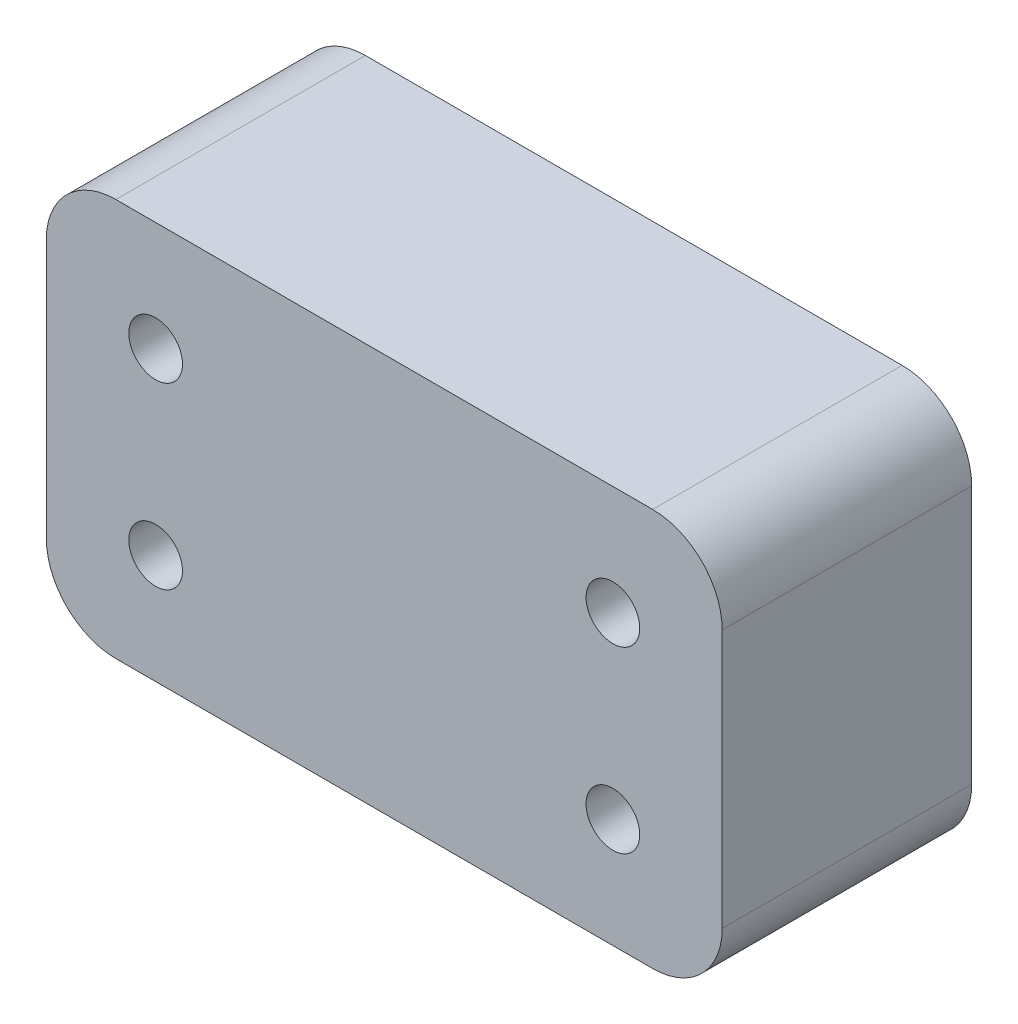
SolidWorks part; units mm, degrees
ref_plane "Front Plane" through (0, 0, 0) normal (0, 0, 1) x (1, 0, 0)
ref_plane "Top Plane" through (0, 0, 0) normal (0, 1, 0) x (1, 0, 0)
ref_plane "Right Plane" through (0, 0, 0) normal (1, 0, 0) x (0, 0, -1)
sketch "Sketch1" plane through (0, 0, 0) normal (0, 0, 1) x (1, 0, 0)
  line L0 (38.9055, 79) -> (-21.0984, 79)
  line L1 (38.9055, 79) -> (38.9055, 47)
  line L4 (-21.0945, 79) -> (-21.0945, 47)
  line L6 (38.9055, 47) -> (-21.0945, 47)
  circle A4 centre (31.9055, 72) radius 2.75 construction
  dimension "D1" = 7
  dimension "D2" = 7
extrude "Boss-Extrude1" add sketch "Sketch1" along normal blind 25.1 contours L6 L1 L0 L4
hole_wizard "M5 Clearance Hole1" positions "Sketch2" profile "Sketch3" hole size "M5" standard "ISO" end condition through all
sketch "Sketch2" plane through (0, 0, 25.1) normal (0, 0, -1) x (-1, 0, 0)
  line L0 (-38.9055, 79) -> (-38.9055, 47) construction
  line L1 (-38.9055, 47) -> (21.0945, 47) construction
  point P0 (-31.9055, 72)
  point P2 (-31.9055, 54)
  point P4 (14.0945, 54)
  point P6 (14.0945, 72)
  dimension "D1" = 46
  dimension "D2" = 18
  dimension "D3" = 46
  dimension "D4" = 18
  dimension "D5" = 7
  dimension "D6" = 7
sketch "Sketch3" plane through (31.9055, 72, 25.1) normal (1, 0, 0) x (0, -1, 0)
  line L0 (0, 0) -> (0, 25.1)
  line L1 (0, 25.1) -> (2.7, 25.1)
  line L2 (2.7, 25.1) -> (2.7, 0)
  line L5 (2.7, 0) -> (0, 0)
  line L11 (0, -6.35) -> (0, 107.95) construction
  dimension "Thru Hole Dia." = 5.4
  dimension "Thru Hole Depth" = 25.1
fillet "Fillet1" radius 3 4 edges at (38.9055, 47, 12.55) (-21.0945, 47, 12.55) (38.9055, 79, 12.55) (-21.0945, 79, 12.55)
sketch "Sketch4" plane through (0, 0, 25.1) normal (0, 0, 1) x (1, 0, 0)
  line L8 (42.9055, 50) -> (42.9055, 76)
  line L9 (35.9055, 83) -> (-18.0945, 83)
  line L10 (-25.0945, 76) -> (-25.0945, 50)
  line L11 (-18.0945, 43) -> (35.9055, 43)
  line L12 (42.9055, 50) -> (42.9055, 76)
  line L13 (35.9055, 83) -> (-18.0945, 83)
  line L14 (-25.0945, 76) -> (-25.0945, 50)
  line L15 (-18.0945, 43) -> (35.9055, 43)
  line L17 (35.9055, 79) -> (-18.0945, 79)
  line L18 (38.9055, 50) -> (38.9055, 76)
  line L19 (-18.0945, 47) -> (35.9055, 47)
  line L20 (-21.0945, 76) -> (-21.0945, 50)
  line L21 (35.9055, 79) -> (-18.0945, 79)
  line L22 (38.9055, 50) -> (38.9055, 76)
  line L23 (-18.0945, 47) -> (35.9055, 47)
  line L24 (-21.0945, 76) -> (-21.0945, 50)
  arc A8 (42.9055, 76) -> (35.9055, 83) centre (35.9055, 76) ccw
  arc A9 (-18.0945, 83) -> (-25.0945, 76) centre (-18.0945, 76) ccw
  arc A10 (-25.0945, 50) -> (-18.0945, 43) centre (-18.0945, 50) ccw
  arc A11 (35.9055, 43) -> (42.9055, 50) centre (35.9055, 50) ccw
  arc A12 (42.9055, 76) -> (35.9055, 83) centre (35.9055, 76) ccw
  arc A13 (-18.0945, 83) -> (-25.0945, 76) centre (-18.0945, 76) ccw
  arc A14 (-25.0945, 50) -> (-18.0945, 43) centre (-18.0945, 50) ccw
  arc A15 (35.9055, 43) -> (42.9055, 50) centre (35.9055, 50) ccw
  arc A17 (38.9055, 76) -> (35.9055, 79) centre (35.9055, 76) ccw
  arc A18 (35.9055, 47) -> (38.9055, 50) centre (35.9055, 50) ccw
  arc A19 (-21.0945, 50) -> (-18.0945, 47) centre (-18.0945, 50) ccw
  arc A20 (-18.0945, 79) -> (-21.0945, 76) centre (-18.0945, 76) ccw
  arc A21 (38.9055, 76) -> (35.9055, 79) centre (35.9055, 76) ccw
  arc A22 (35.9055, 47) -> (38.9055, 50) centre (35.9055, 50) ccw
  arc A23 (-21.0945, 50) -> (-18.0945, 47) centre (-18.0945, 50) ccw
  arc A24 (-18.0945, 79) -> (-21.0945, 76) centre (-18.0945, 76) ccw
  dimension "D1" = 4
  dimension "D2" = 0
extrude "Boss-Extrude2" add sketch "Sketch4" against normal up to surface (25.1 mm away) up to face at (34.6055, 72, 0)
